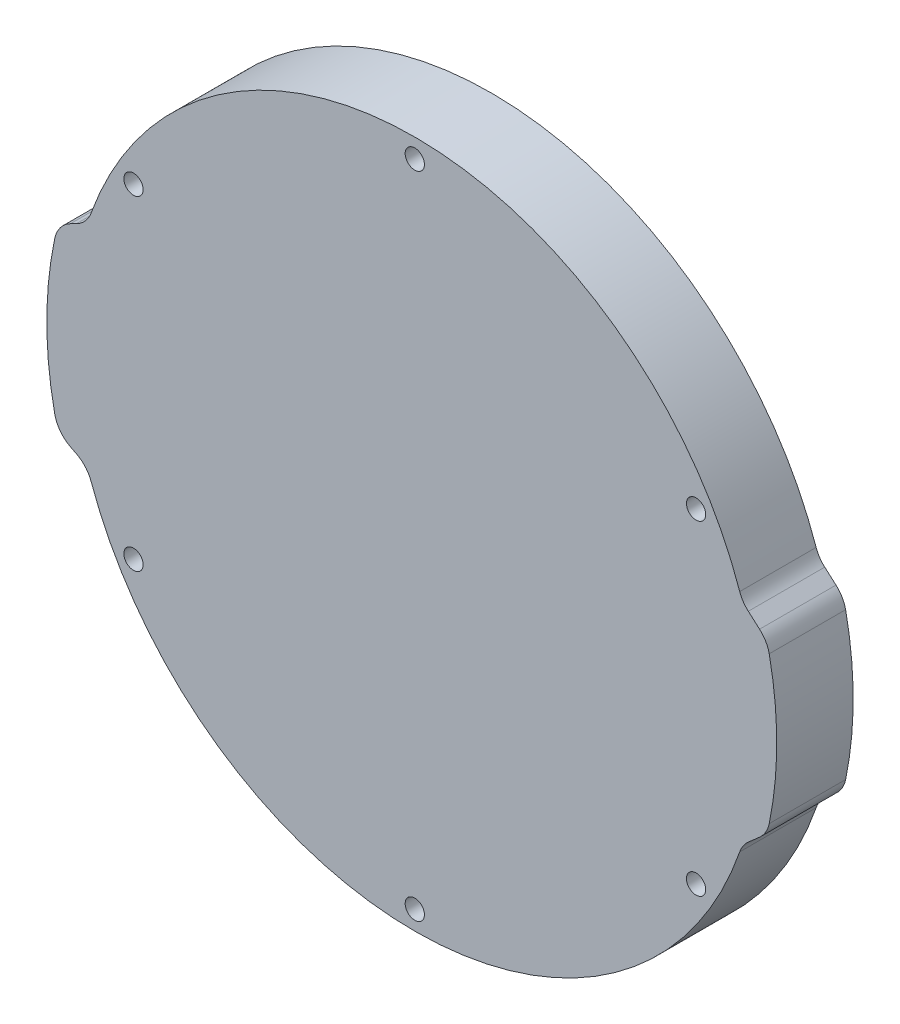
SolidWorks part; units mm, degrees
material "ABS PC"
ref_plane "Front Plane" through (0, 0, 0) normal (0, 0, 1) x (1, 0, 0)
ref_plane "Top Plane" through (0, 0, 0) normal (0, 1, 0) x (1, 0, 0)
ref_plane "Right Plane" through (0, 0, 0) normal (1, 0, 0) x (0, 0, -1)
sketch "Sketch1" plane through (0, 0, 0) normal (0, 0, 1) x (1, 0, 0)
  line L0 (-59.2817, 15) -> (-54.4047, 17.5)
  line L1 (-59.2817, -15) -> (-54.4047, -17.5)
  line L2 (58.5251, 13.8865) -> (54.4047, 17.5)
  line L3 (58.5251, -13.8865) -> (54.4047, -17.5)
  line L4 (0, 0) -> (46.7437, 26.9875) construction
  line L5 (46.7437, 26.9875) -> (49.4934, 28.575) construction
  line L6 (0, 53.975) -> (0, 0) construction
  arc A0 (-54.4047, -17.5) -> (54.4047, -17.5) centre (0, 0) ccw
  circle A1 centre (0, 53.975) radius 1.6
  circle A2 centre (46.7437, 26.9875) radius 1.6
  circle A3 centre (46.7437, -26.9875) radius 1.6
  circle A4 centre (0, -53.975) radius 1.6
  circle A5 centre (-46.7437, -26.9875) radius 1.6
  circle A6 centre (-46.7437, 26.9875) radius 1.6
  arc A7 (-59.2817, 15) -> (-59.2817, -15) centre (0, 0) ccw
  arc A8 (58.5251, 13.8865) -> (58.5251, -13.8865) centre (0, 0) cw
  arc A9 (54.4047, 17.5) -> (-54.4047, 17.5) centre (0, 0) ccw
  point P17 (0, 0)
  point P19 (-61.15, 0)
  point P24 (60.15, 0)
  dimension "D1" = 114.3
  dimension "D2" = 3.175
  dimension "D3" = 3.2
  dimension "D6" = 4
  dimension "D8" = 3
  dimension "D5" = 35
  dimension "D7" = 30
  dimension "D9" = 3.175
  dimension "D10" = 60
  dimension "D4" = 6
extrude "Boss-Extrude1" add sketch "Sketch1" along normal blind 12.7
fillet "Fillet1" radius 5 8 edges at (54.4047, 17.5, 6.35) (58.5251, 13.8865, 6.35) (58.5251, -13.8865, 6.35) (54.4047, -17.5, 6.35) (-54.4047, -17.5, 6.35) (-59.2817, -15, 6.35) (-54.4047, 17.5, 6.35) (-59.2817, 15, 6.35)
